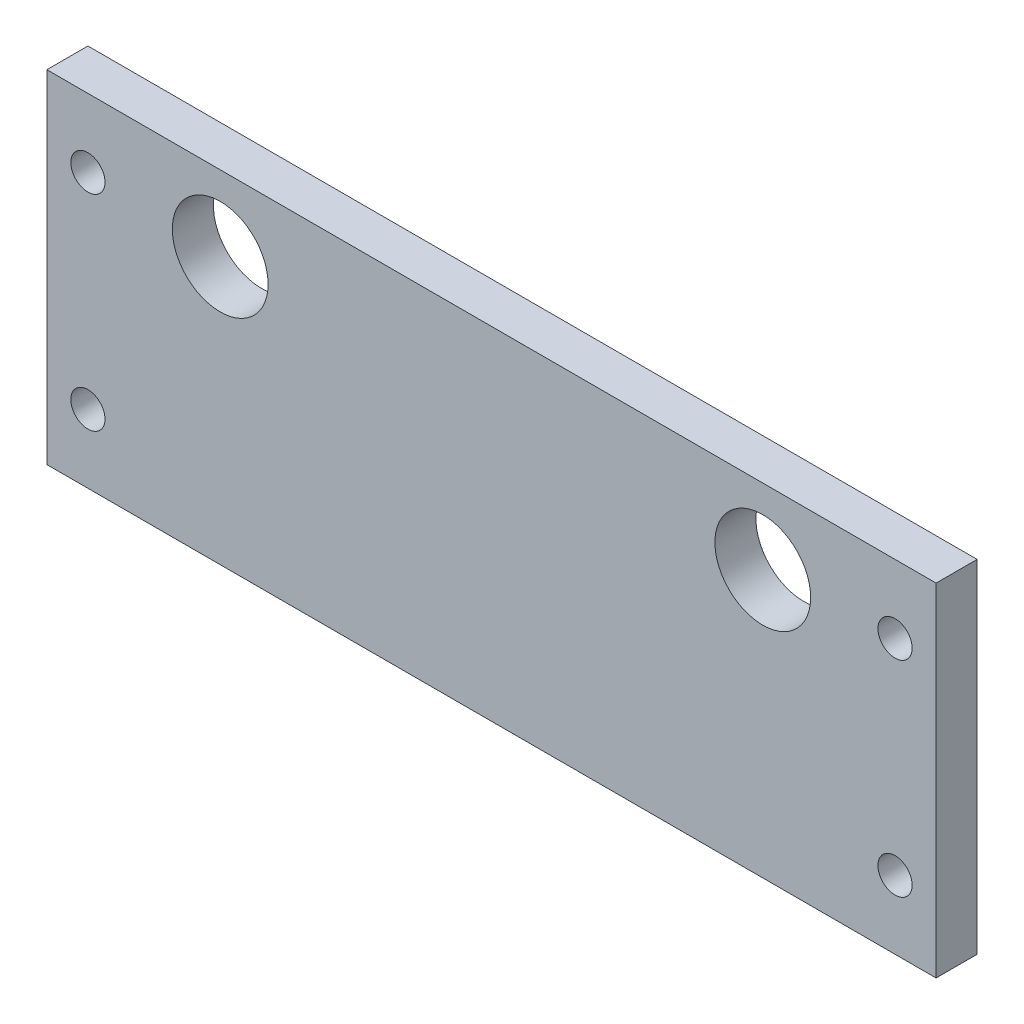
SolidWorks part; units mm, degrees
ref_plane "正面" through (0, 0, 0) normal (0, 0, 1) x (1, 0, 0)
ref_plane "平面" through (0, 0, 0) normal (0, 1, 0) x (1, 0, 0)
ref_plane "右側面" through (0, 0, 0) normal (1, 0, 0) x (0, 0, -1)
sketch "ｽｹｯﾁ1" plane through (0, 0, 0) normal (0, 0, 1) x (1, 0, 0)
  line L0 (0, 0) -> (0, 7)
  line L1 (-32.5, 12.5) -> (32.5, 12.5)
  line L2 (-32.5, 12.5) -> (-32.5, -12.5)
  line L3 (-32.5, -12.5) -> (32.5, -12.5)
  line L4 (32.5, 12.5) -> (32.5, -12.5)
  line L5 (-32.5, 12.5) -> (32.5, -12.5) construction
  line L6 (-32.5, -12.5) -> (32.5, 12.5) construction
  line L7 (0, 7) -> (19.83, 7)
  line L8 (0, 7) -> (-19.83, 7)
  circle A0 centre (-19.83, 7) radius 3.5
  circle A1 centre (19.83, 7) radius 3.5
  point P0 (0, 0)
  dimension "D3" = 7
  dimension "D4" = 7
  dimension "D1" = 19.83
  dimension "D2" = 19.83
  dimension "D5" = 25
  dimension "D6" = 65
  dimension "D7" = 7
extrude "ﾎﾞｽ - 押し出し1" add sketch "ｽｹｯﾁ1" along normal blind 3
sketch "ｽｹｯﾁ2" plane through (0, 0, 3) normal (0, 0, 1) x (1, 0, 0)
  line L0 (-32.5, 12.5) -> (-32.5, -12.5) construction
  line L1 (-32.5, 12.5) -> (-29.5, 12.5)
  line L2 (-32.5, 12.5) -> (-32.5, 7.5)
  line L3 (-32.5, 7.5) -> (-29.5, 7.5)
  line L4 (-29.5, 12.5) -> (-29.5, 7.5)
  line L5 (-32.5, -12.5) -> (-29.5, -12.5)
  line L6 (-32.5, -12.5) -> (-32.5, -7.5)
  line L7 (-32.5, -7.5) -> (-29.5, -7.5)
  line L8 (-29.5, -12.5) -> (-29.5, -7.5)
  line L9 (-32.5, -12.5) -> (32.5, -12.5) construction
  line L10 (32.5, 12.5) -> (32.5, -12.5) construction
  line L11 (32.5, -12.5) -> (29.5, -12.5)
  line L12 (32.5, -12.5) -> (32.5, -7.5)
  line L13 (32.5, -7.5) -> (29.5, -7.5)
  line L14 (29.5, -12.5) -> (29.5, -7.5)
  line L16 (32.5, 12.5) -> (29.5, 12.5)
  line L17 (32.5, 12.5) -> (32.5, 7.5)
  line L18 (32.5, 7.5) -> (29.5, 7.5)
  line L19 (29.5, 12.5) -> (29.5, 7.5)
  circle A0 centre (-29.5, 7.5) radius 1.6
  circle A1 centre (-29.5, -7.5) radius 1.6
  circle A2 centre (29.5, 7.5) radius 1.6
  circle A3 centre (29.5, -7.5) radius 1.6
  dimension "D9" = 3.2
  dimension "D10" = 3.2
  dimension "D11" = 3.2
  dimension "D12" = 3.2
  dimension "D1" = 3
  dimension "D2" = 5
  dimension "D3" = 3
  dimension "D4" = 5
  dimension "D5" = 3
  dimension "D6" = 5
  dimension "D7" = 3
  dimension "D8" = 5
hole_wizard "M3x0.5 ねじ穴1" positions "3Dｽｹｯﾁ2" profile "ｽｹｯﾁ4" tap size "M3x0.5" standard "JIS"
sketch3d "3Dｽｹｯﾁ2"
  point P0 (-29.5, 7.5, 3)
  point P3 (-29.5, -7.5, 3)
  point P6 (29.5, 7.5, 3)
  point P9 (29.5, -7.5, 3)
sketch "ｽｹｯﾁ4" plane through (-29.5, 7.5, 3) normal (1, 0, 0) x (0, -1, 0)
  line L0 (0, 0) -> (0, 9.2511)
  line L1 (0, 9.2511) -> (1.25, 8.5)
  line L2 (1.25, 8.5) -> (1.25, 0)
  line L5 (1.25, 0) -> (0, 0)
  line L10 (0, 9.2511) -> (-1.25, 8.5) construction
  line L11 (0, -6.35) -> (0, 107.95) construction
  dimension "ねじ下穴ﾄﾞﾘﾙ直径" = 2.5
  dimension "ねじ下穴ﾄﾞﾘﾙの深さ" = 8.5
  dimension "ﾄﾞﾘﾙ角度" = 118
cosmetic thread "穴のねじ山1" parameters "D1"=3, "D2"=3
cosmetic thread "穴のねじ山2" parameters "D1"=3, "D2"=3
cosmetic thread "穴のねじ山3" parameters "D1"=3, "D2"=3
cosmetic thread "穴のねじ山4" parameters "D1"=3, "D2"=3
